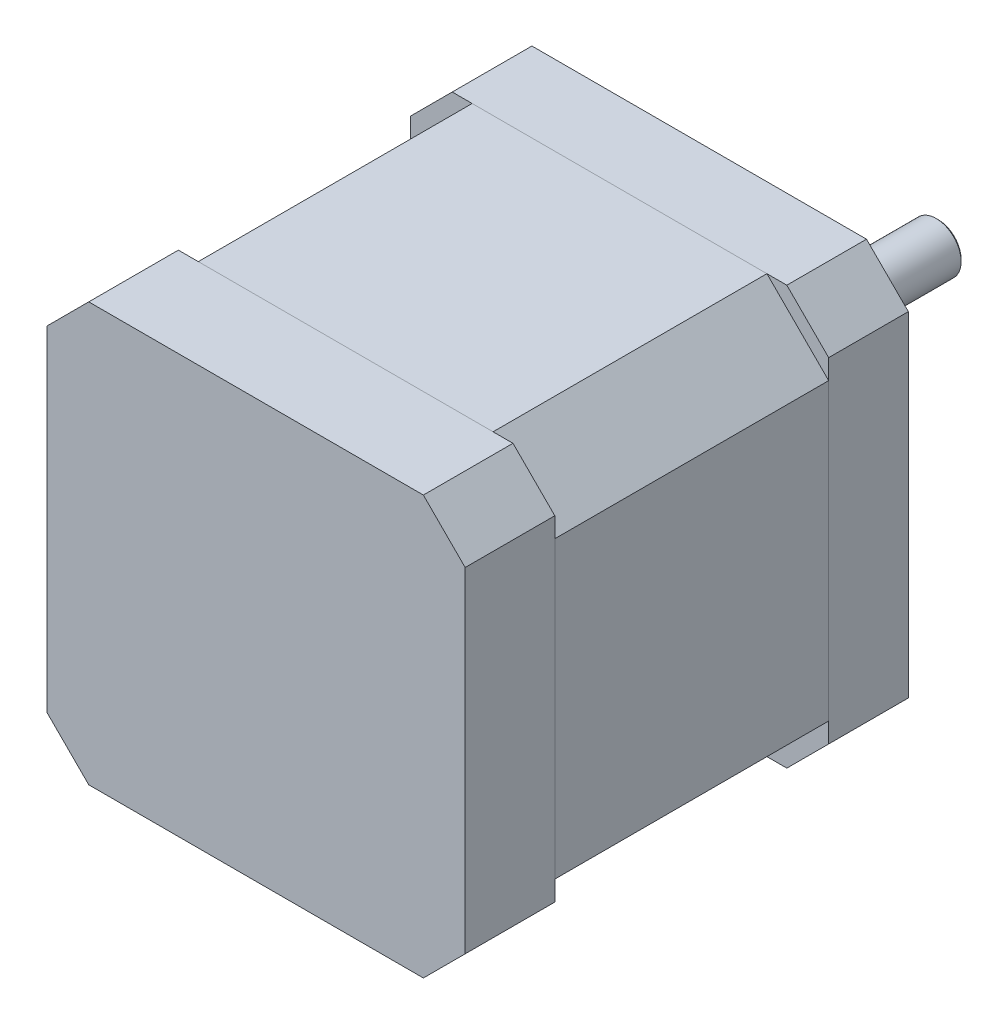
SolidWorks part; units mm, degrees
ref_plane "Plan de face" through (0, 0, 0) normal (0, 0, 1) x (1, 0, 0)
ref_plane "Plan de dessus" through (0, 0, 0) normal (0, 1, 0) x (1, 0, 0)
ref_plane "Plan de droite" through (0, 0, 0) normal (1, 0, 0) x (0, 0, -1)
sketch "Esquisse1" plane through (0, 0, 0) normal (0, 0, 1) x (1, 0, 0)
  line L1 (-21, 21) -> (21, 21)
  line L2 (-21, 21) -> (-21, -21)
  line L3 (-21, -21) -> (21, -21)
  line L4 (21, 21) -> (21, -21)
  line L5 (-21, 21) -> (21, -21) construction
  line L6 (-21, -21) -> (21, 21) construction
  point P0 (0, 0)
  dimension "D1" = 42
  dimension "D2" = 42
extrude "Boss.-Extru.1" add sketch "Esquisse1" along normal blind 8
chamfer "Chanfrein1" distance 4.2 angle 45 4 edges at (-21, -21, 4) (-21, 21, 4) (21, 21, 4) (21, -21, 4)
sketch "Esquisse3" plane through (0, 0, 8) normal (0, 0, 1) x (1, 0, 0)
  line L0 (-21, 14.8) -> (-14.8, 21)
  line L1 (-14.8, 21) -> (14.8, 21)
  line L2 (-21, 14.8) -> (-21, -14.8)
  line L3 (-14.8, -21) -> (14.8, -21)
  line L4 (21, 14.8) -> (21, -14.8)
  line L5 (-21, 21) -> (21, -21) construction
  line L6 (-21, -21) -> (21, 21) construction
  line L7 (14.8, 21) -> (21, 14.8)
  line L8 (14.8, -21) -> (21, -14.8)
  line L9 (-21, -14.8) -> (-14.8, -21)
  point P0 (0, 0)
  dimension "D1" = 42
  dimension "D2" = 42
extrude "Boss.-Extru.2" add sketch "Esquisse3" along normal blind 27.5 separate body
sketch "Esquisse4" plane through (0, 0, 35.5) normal (0, 0, 1) x (1, 0, 0)
  line L1 (-21, -21) -> (21, -21)
  line L2 (-21, -21) -> (-21, 21)
  line L3 (-21, 21) -> (21, 21)
  line L4 (21, -21) -> (21, 21)
  line L5 (-21, -21) -> (21, 21) construction
  line L6 (-21, 21) -> (21, -21) construction
  point P0 (0, 0)
  dimension "D1" = 42
  dimension "D2" = 42
extrude "Boss.-Extru.3" add sketch "Esquisse4" along normal blind 9 separate body
chamfer "Chanfrein3" distance 4.2 angle 45 4 edges at (21, 21, 40) (21, -21, 40) (-21, -21, 40) (-21, 21, 40)
sketch "Esquisse5" plane through (0, 0, 0) normal (0, 0, -1) x (-1, 0, 0)
  circle A0 centre (0, 0) radius 11
  dimension "D1" = 22
extrude "Boss.-Extru.4" add sketch "Esquisse5" along normal blind 2
sketch "Esquisse6" plane through (0, 0, -2) normal (0, 0, -1) x (-1, 0, 0)
  circle A0 centre (0, 0) radius 4.5
  dimension "D1" = 9
extrude "Enlèv. mat.-Extru.1" cut sketch "Esquisse6" against normal blind 3
sketch "Esquisse7" plane through (0, 0, 1) normal (0, 0, -1) x (-1, 0, 0)
  circle A0 centre (0, 0) radius 2.5
  dimension "D1" = 5
extrude "Boss.-Extru.5" add sketch "Esquisse7" along normal blind 25
chamfer "Chanfrein4" distance 0.2 angle 45 1 edges at (-2.5, 0, -24)
sketch "Esquisse8" plane through (0, 0, 0) normal (0, 0, -1) x (-1, 0, 0)
  line L1 (-15.5, 15.5) -> (15.5, 15.5) construction
  line L2 (-15.5, 15.5) -> (-15.5, -15.5) construction
  line L3 (-15.5, -15.5) -> (15.5, -15.5) construction
  line L4 (15.5, 15.5) -> (15.5, -15.5) construction
  line L5 (-15.5, 15.5) -> (15.5, -15.5) construction
  line L6 (-15.5, -15.5) -> (15.5, 15.5) construction
  circle A0 centre (-15.5, 15.5) radius 1.5
  circle A1 centre (15.5, 15.5) radius 1.5
  circle A2 centre (15.5, -15.5) radius 1.5
  circle A3 centre (-15.5, -15.5) radius 1.5
  point P0 (0, 0)
  dimension "D3" = 3
  dimension "D1" = 31
  dimension "D2" = 31
extrude "Enlèv. mat.-Extru.2" cut sketch "Esquisse8" against normal blind 5
chamfer "Chanfrein5" distance 0.2 angle 45 4 edges at (14, -15.5, 0) (-17, -15.5, 0) (-17, 15.5, 0) (14, 15.5, 0)
sketch "Esquisse9" plane through (-21, 0, 0) normal (-1, 0, 0) x (0, 0, 1)
  line L0 (39, 0) -> (35.5, 0) construction
  line L1 (35.5, -4) -> (42.5, -4)
  line L2 (35.5, -4) -> (35.5, 4)
  line L3 (35.5, 4) -> (42.5, 4)
  line L4 (42.5, -4) -> (42.5, 4)
  line L5 (35.5, -4) -> (42.5, 4) construction
  line L6 (35.5, 4) -> (42.5, -4) construction
  line L7 (35.5, 16.8) -> (35.5, -16.8) construction
  point P0 (39, 0)
  dimension "D1" = 7
  dimension "D2" = 8
extrude "Enlèv. mat.-Extru.3" cut sketch "Esquisse9" against normal blind 2
